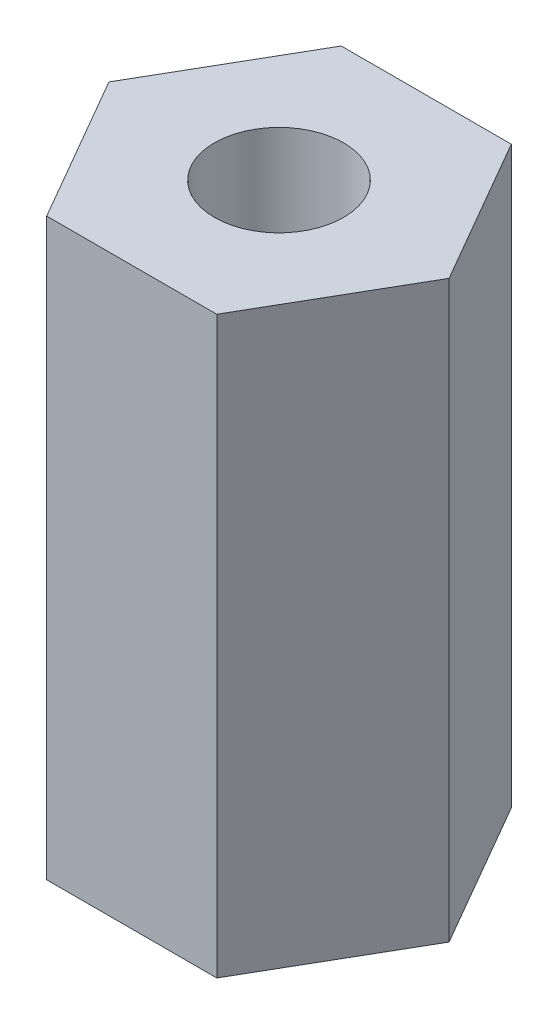
SolidWorks part; units mm, degrees
material "1060 Alloy"
ref_plane "Front Plane" through (0, 0, 0) normal (0, 0, 1) x (1, 0, 0)
ref_plane "Top Plane" through (0, 0, 0) normal (0, 1, 0) x (1, 0, 0)
ref_plane "Right Plane" through (0, 0, 0) normal (1, 0, 0) x (0, 0, -1)
sketch "Sketch1" plane through (0, 0, 0) normal (0, 1, 0) x (1, 0, 0)
  line L1 (5, 0) -> (2.5, 4.3301)
  line L2 (2.5, 4.3301) -> (-2.5, 4.3301)
  line L3 (-2.5, 4.3301) -> (-5, 0)
  line L4 (-5, 0) -> (-2.5, -4.3301)
  line L5 (-2.5, -4.3301) -> (2.5, -4.3301)
  line L6 (2.5, -4.3301) -> (5, 0)
  circle A0 centre (0, 0) radius 4.3301 construction
  dimension "D1" = 5
extrude "Boss-Extrude1" add sketch "Sketch1" along normal blind 16.9
sketch "Sketch3" plane through (0, 16.9, 0) normal (0, 1, 0) x (1, 0, 0)
  circle A0 centre (0, 0) radius 1.9
  dimension "D1" = 3.8
extrude "Cut-Extrude1" cut sketch "Sketch3" against normal through all
